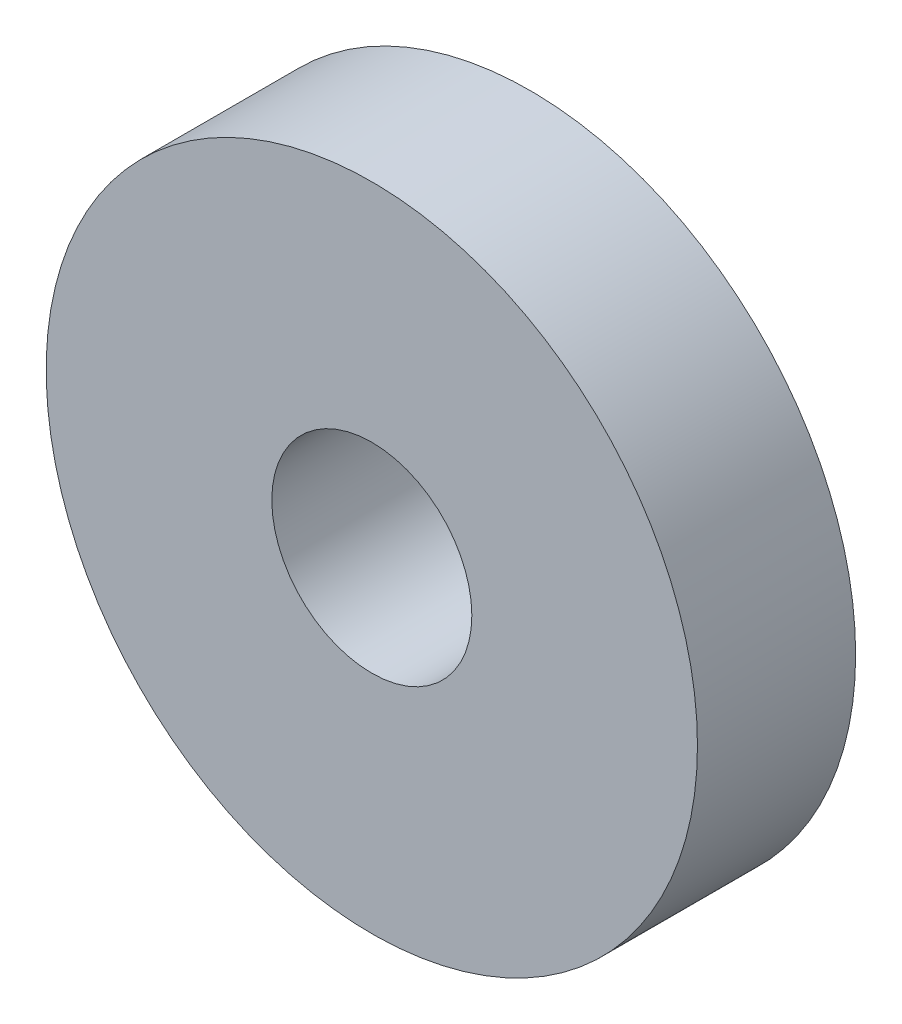
SolidWorks part; units mm, degrees
ref_plane "Front Plane" through (0, 0, 0) normal (0, 0, 1) x (1, 0, 0)
ref_plane "Top Plane" through (0, 0, 0) normal (0, 1, 0) x (1, 0, 0)
ref_plane "Right Plane" through (0, 0, 0) normal (1, 0, 0) x (0, 0, -1)
sketch "Sketch1" plane through (0, 0, 0) normal (0, 0, 1) x (1, 0, 0)
  circle A0 centre (0, 0) radius 7
  circle A1 centre (0, 0) radius 2.15
  dimension "OD" = 14
  dimension "ID1" = 4.3
extrude "Boss-Extrude1" add sketch "Sketch1" along normal blind 3.4
